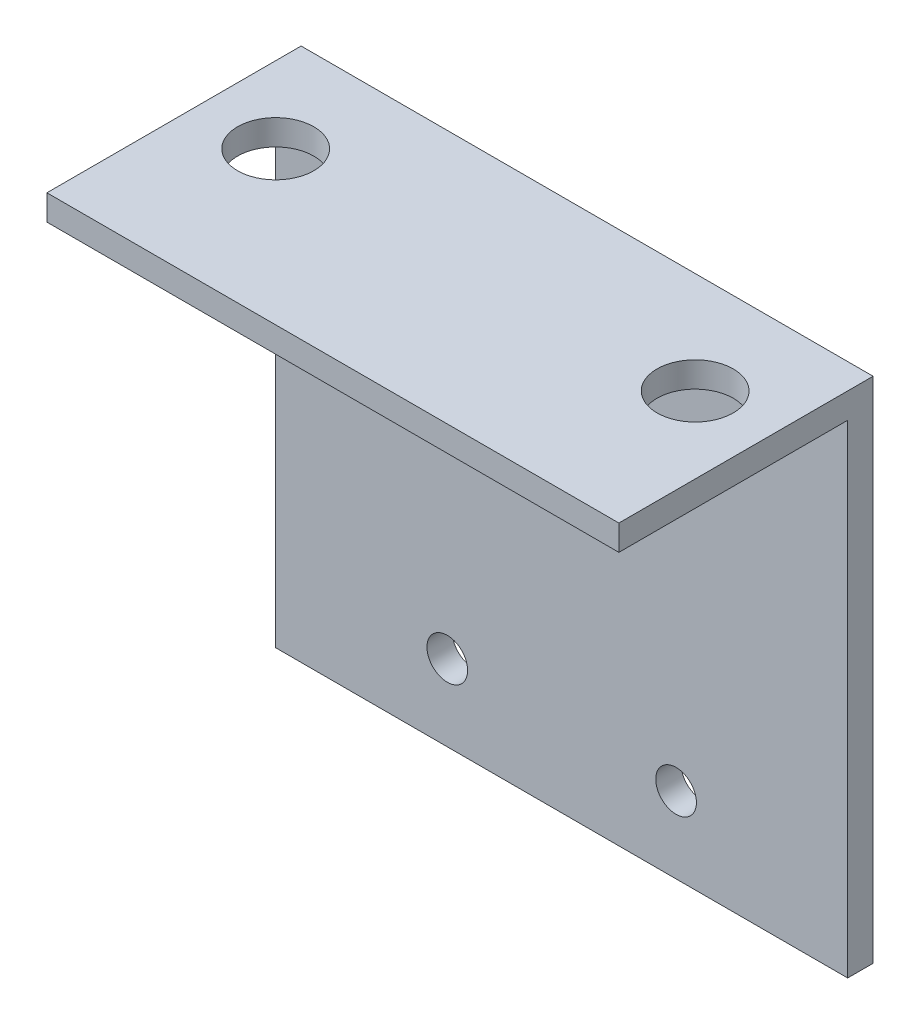
SolidWorks part; units mm, degrees
ref_plane "正面" through (0, 0, 0) normal (0, 0, 1) x (1, 0, 0)
ref_plane "平面" through (0, 0, 0) normal (0, 1, 0) x (1, 0, 0)
ref_plane "右側面" through (0, 0, 0) normal (1, 0, 0) x (0, 0, -1)
sketch "ｽｹｯﾁ1" plane through (0, 0, 0) normal (1, 0, 0) x (0, 0, -1)
  line L0 (-18, 40) -> (-18, 38)
  line L1 (-18, 38) -> (0, 38)
  line L2 (0, 38) -> (0, 0)
  line L3 (0, 0) -> (2, 0)
  line L4 (2, 0) -> (2, 40)
  line L5 (2, 40) -> (-18, 40)
  dimension "D1" = 2
  dimension "D2" = 20
  dimension "D3" = 40
  dimension "D4" = 2
extrude "ﾎﾞｽ - 押し出し1" add sketch "ｽｹｯﾁ1" along normal blind 45
sketch "ｽｹｯﾁ2" plane through (0, 38, 0) normal (0, -1, 0) x (1, 0, 0)
  line L0 (0, 6) -> (45, 6) construction
  line L1 (0, 18) -> (0, 0) construction
  line L2 (45, 18) -> (45, 0) construction
  line L3 (45, 0) -> (0, 0) construction
  circle A0 centre (6, 6) radius 3
  circle A1 centre (39, 6) radius 3
  dimension "D1" = 6
  dimension "D2" = 6
  dimension "D4" = 6
  dimension "D3" = 6
  dimension "D5" = 6
extrude "ｶｯﾄ - 押し出し1" cut sketch "ｽｹｯﾁ2" against normal through all
sketch "ｽｹｯﾁ3" plane through (0, 0, 0) normal (0, 0, 1) x (1, 0, 0)
  line L5 (45, 0) -> (0, 0) construction
  line L7 (0, 12) -> (45, 12) construction
  line L8 (0, 12) -> (0, 0) construction
  line L9 (0, 0) -> (45, 0) construction
  line L10 (45, 12) -> (45, 0) construction
  line L11 (0, 12) -> (45, 0) construction
  line L12 (0, 0) -> (45, 12) construction
  line L13 (0, 38) -> (0, 0) construction
  line L14 (0, 12) -> (45, 38) construction
  line L15 (0, 38) -> (45, 12) construction
  circle A1 centre (22.5, 25) radius 2.6
  point P0 (22.5, 6)
  point P14 (22.5, 25)
  dimension "D2" = 5.2
  dimension "D1" = 12
extrude "ｶｯﾄ - 押し出し2" cut sketch "ｽｹｯﾁ3" against normal through all
sketch "ｽｹｯﾁ4" plane through (0, 0, 0) normal (0, 0, 1) x (1, 0, 0)
  line L0 (0, 38) -> (0, 0) construction
  line L1 (45, 38) -> (45, 0) construction
  line L2 (45, 0) -> (0, 0) construction
  circle A0 centre (13.5, 6) radius 1.6
  circle A1 centre (31.5, 6) radius 1.6
  dimension "D1" = 13.5
  dimension "D5" = 3.2
  dimension "D2" = 13.5
  dimension "D3" = 6
  dimension "D4" = 6
extrude "ｶｯﾄ - 押し出し3" cut sketch "ｽｹｯﾁ4" against normal through all
